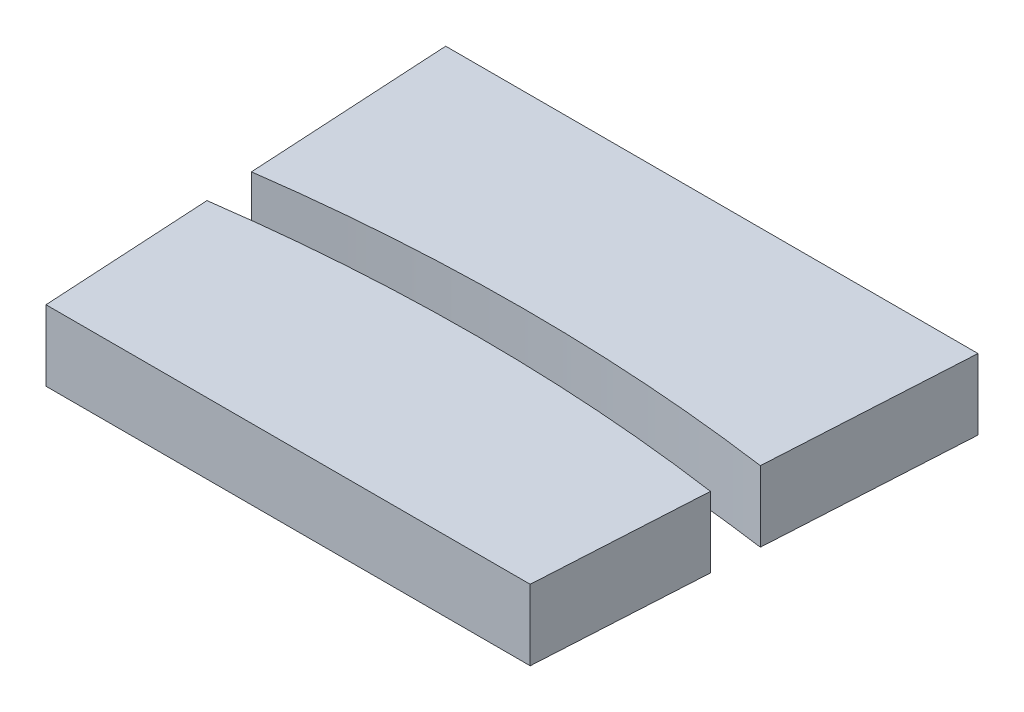
SolidWorks part; units mm, degrees
ref_plane "Front Plane" through (0, 0, 0) normal (0, 0, 1) x (1, 0, 0)
ref_plane "Top Plane" through (0, 0, 0) normal (0, 1, 0) x (1, 0, 0)
ref_plane "Right Plane" through (0, 0, 0) normal (1, 0, 0) x (0, 0, -1)
sketch "Sketch1" plane through (0, 0, 0) normal (0, 1, 0) x (1, 0, 0)
  line L0 (-11.59, 91.5) -> (-10, 63.5)
  line L5 (-11.59, 91.5) -> (0, 91.5)
  line L6 (0, 91.5) -> (0, 63.5)
  line L7 (0, 63.5) -> (-10, 63.5)
  point P4 (0, 77.5)
  dimension "D1" = 28
  dimension "D2" = 77.5
  dimension "D3" = 3.25
  dimension "D4" = 10
extrude "Boss-Extrude1" add sketch "Sketch1" along normal blind 3
sketch "Sketch55" plane through (0, 3, 0) normal (0, 1, 0) x (1, 0, 0)
  line L0 (-10.2839, 68.5) -> (0, 68.5)
  line L1 (-11.306, 86.5) -> (-11.59, 91.5)
  line L2 (-11.59, 91.5) -> (0, 91.5)
  line L3 (0, 63.5) -> (0, 91.5) construction
  line L5 (0, 86.5) -> (-11.306, 86.5)
  line L7 (-11.59, 91.5) -> (-10, 63.5) construction
  line L8 (-11.59, 91.5) -> (-10, 63.5) construction
  line L9 (0, 91.5) -> (0, 86.5)
  line L10 (0, 68.5) -> (0, 63.5)
  line L11 (0, 63.5) -> (-10, 63.5)
  line L12 (-10, 63.5) -> (-10.2839, 68.5)
  dimension "D1" = 5
  dimension "D2" = 18
extrude "Cut-Extrude10" cut sketch "Sketch55" against normal through all both and the other way through all
mirror "Mirror14" about plane through (0, 0, 0) normal (1, 0, 0) of bodies 126 131
sketch "Sketch56" plane through (0, 3, 0) normal (0, 1, 0) x (1, 0, 0)
  line L0 (-11.306, 86.5) -> (-10.2839, 68.5) construction
  line L1 (11.306, 86.5) -> (10.2839, 68.5) construction
  line L2 (-10.8297, 77.7494) -> (-10.6955, 75.7486)
  line L3 (10.6955, 75.7486) -> (10.8093, 77.7522)
  arc A0 (-10.8297, 77.7494) -> (10.8093, 77.7522) centre (0, 0) cw
  arc A1 (-10.6955, 75.7486) -> (10.6955, 75.7486) centre (0, 0) cw
  dimension "D1" = 78.5
  dimension "D2" = 76.5
extrude "Cut-Extrude11" cut sketch "Sketch56" against normal through all both and the other way through all
